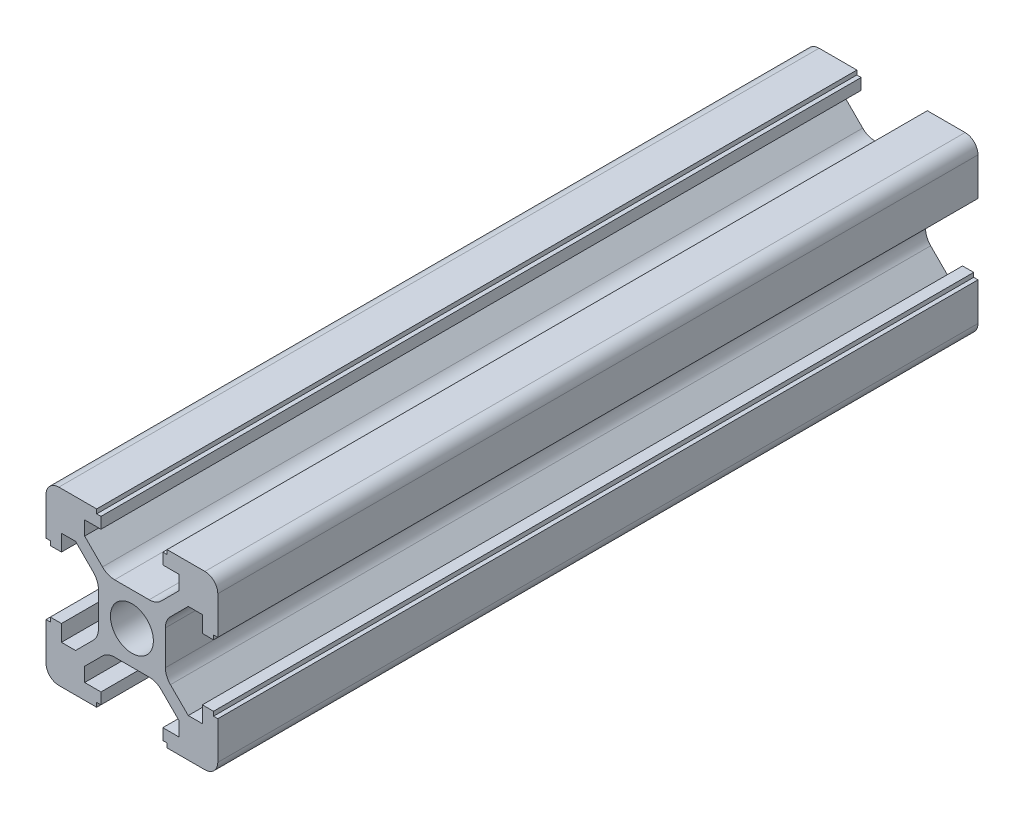
SolidWorks part; units mm, degrees
ref_plane "Front Plane" through (0, 0, 0) normal (0, 0, 1) x (1, 0, 0)
ref_plane "Top Plane" through (0, 0, 0) normal (0, 1, 0) x (1, 0, 0)
ref_plane "Right Plane" through (0, 0, 0) normal (1, 0, 0) x (0, 0, -1)
sketch "Sketch1" plane through (0, 0, 0) normal (0, 0, 1) x (1, 0, 0)
  line L0 (10, -4.1) -> (10, -8.5)
  line L1 (4.1, 10) -> (8.5, 10)
  line L2 (8.5, -10) -> (4.1, -10)
  line L3 (-8.5, -10) -> (-4.1, -10)
  line L4 (10, 8.5) -> (10, 4.1)
  line L7 (8.5, 10) -> (4.1, 10)
  line L8 (5.5, 6.5607) -> (3.4251, 4.4858)
  line L9 (8.5, 10) -> (4.1, 10)
  line L10 (3.9, 2.0109) -> (3.9, -2.0109)
  line L11 (2.0109, -3.9) -> (-2.0109, -3.9)
  line L12 (-3.9, -2.0109) -> (-3.9, 2.0109)
  line L13 (-2.0109, 3.9) -> (2.8393, 3.9)
  line L14 (2.5, 0) -> (22.2403, 0) construction
  line L15 (3.6, 9.5) -> (3.6, 8.2)
  line L16 (9.5, 3.6) -> (8.2, 3.6)
  line L17 (8.2, 3.6) -> (8.2, 5.5)
  line L18 (8.2, 5.5) -> (6.5607, 5.5)
  line L19 (10, -4.1) -> (10, -8.5)
  line L20 (4.1, 9.5) -> (3.6, 9.5)
  line L21 (4.1, 10) -> (4.1, 9.5)
  line L22 (8.5, 10) -> (4.1, 10)
  line L23 (10, 4.1) -> (9.5, 4.1)
  line L24 (9.5, 4.1) -> (9.5, 3.6)
  line L25 (5.5, 8.2) -> (5.5, 6.5607)
  line L26 (3.6, 8.2) -> (5.5, 8.2)
  line L27 (4.4858, 3.4251) -> (6.5607, 5.5)
  line L28 (10, -8.5) -> (10, -4.1)
  line L29 (6.5607, -5.5) -> (4.4858, -3.4251)
  line L30 (10, -8.5) -> (10, -4.1)
  line L31 (2.0109, -3.9) -> (-2.0109, -3.9)
  line L32 (3.9, 2.8393) -> (3.9, -2.0109)
  line L33 (9.5, -3.6) -> (8.2, -3.6)
  line L34 (3.6, -9.5) -> (3.6, -8.2)
  line L35 (3.6, -8.2) -> (5.5, -8.2)
  line L36 (5.5, -8.2) -> (5.5, -6.5607)
  line L37 (9.5, -4.1) -> (9.5, -3.6)
  line L38 (10, -4.1) -> (9.5, -4.1)
  line L39 (10, -8.5) -> (10, -4.1)
  line L40 (4.1, -10) -> (4.1, -9.5)
  line L41 (4.1, -9.5) -> (3.6, -9.5)
  line L42 (8.2, -5.5) -> (6.5607, -5.5)
  line L43 (8.2, -3.6) -> (8.2, -5.5)
  line L44 (3.4251, -4.4858) -> (5.5, -6.5607)
  line L45 (-4.1, -10) -> (-8.5, -10)
  line L46 (-10, -8.5) -> (-10, -4.1)
  line L47 (-8.5, -10) -> (-4.1, -10)
  line L48 (-5.5, -6.5607) -> (-3.4251, -4.4858)
  line L49 (-8.5, -10) -> (-4.1, -10)
  line L50 (-3.9, -2.0109) -> (-3.9, 2.0109)
  line L51 (2.0109, -3.9) -> (-2.0109, -3.9)
  line L52 (-3.6, -9.5) -> (-3.6, -8.2)
  line L53 (-9.5, -3.6) -> (-8.2, -3.6)
  line L54 (-8.2, -3.6) -> (-8.2, -5.5)
  line L55 (-8.2, -5.5) -> (-6.5607, -5.5)
  line L56 (-4.1, -9.5) -> (-3.6, -9.5)
  line L57 (-4.1, -10) -> (-4.1, -9.5)
  line L58 (-8.5, -10) -> (-4.1, -10)
  line L59 (-10, -4.1) -> (-9.5, -4.1)
  line L60 (-9.5, -4.1) -> (-9.5, -3.6)
  line L61 (-5.5, -8.2) -> (-5.5, -6.5607)
  line L62 (-3.6, -8.2) -> (-5.5, -8.2)
  line L63 (-4.4858, -3.4251) -> (-6.5607, -5.5)
  line L64 (-10, 4.1) -> (-10, 8.5)
  line L65 (-8.5, 10) -> (-4.1, 10)
  line L66 (-10, 8.5) -> (-10, 4.1)
  line L67 (-6.5607, 5.5) -> (-4.4858, 3.4251)
  line L68 (-10, 8.5) -> (-10, 4.1)
  line L69 (-2.0109, 3.9) -> (2.0109, 3.9)
  line L70 (-3.9, -2.0109) -> (-3.9, 2.0109)
  line L71 (-9.5, 3.6) -> (-8.2, 3.6)
  line L72 (-3.6, 9.5) -> (-3.6, 8.2)
  line L73 (-3.6, 8.2) -> (-5.5, 8.2)
  line L74 (-5.5, 8.2) -> (-5.5, 6.5607)
  line L75 (-9.5, 4.1) -> (-9.5, 3.6)
  line L76 (-10, 4.1) -> (-9.5, 4.1)
  line L77 (-10, 8.5) -> (-10, 4.1)
  line L78 (-4.1, 10) -> (-4.1, 9.5)
  line L79 (-4.1, 9.5) -> (-3.6, 9.5)
  line L80 (-8.2, 5.5) -> (-6.5607, 5.5)
  line L81 (-8.2, 3.6) -> (-8.2, 5.5)
  line L82 (-3.4251, 4.4858) -> (-5.5, 6.5607)
  line L83 (4.1, -10) -> (8.5, -10)
  arc A0 (2.0109, -3.9) -> (3.4251, -4.4858) centre (2.0109, -5.9) cw
  arc A1 (4.4858, -3.4251) -> (3.9, -2.0109) centre (5.9, -2.0109) cw
  arc A2 (3.9, 2.0109) -> (4.4858, 3.4251) centre (5.9, 2.0109) cw
  arc A3 (2.0109, 3.9) -> (3.4251, 4.4858) centre (2.0109, 5.9) ccw
  arc A4 (-2.0109, 3.9) -> (-3.4251, 4.4858) centre (-2.0109, 5.9) cw
  arc A5 (-4.4858, 3.4251) -> (-3.9, 2.0109) centre (-5.9, 2.0109) cw
  arc A6 (-3.4251, -4.4858) -> (-2.0109, -3.9) centre (-2.0109, -5.9) cw
  arc A7 (-3.9, -2.0109) -> (-4.4858, -3.4251) centre (-5.9, -2.0109) cw
  circle A8 centre (0, 0) radius 2.5
  arc A9 (-8.5, -10) -> (-10, -8.5) centre (-8.5, -8.5) cw
  arc A10 (-10, 8.5) -> (-8.5, 10) centre (-8.5, 8.5) cw
  arc A11 (8.5, 10) -> (10, 8.5) centre (8.5, 8.5) cw
  arc A12 (8.5, -10) -> (10, -8.5) centre (8.5, -8.5) ccw
  point P0 (0, 0)
  point P86 (0, 0)
  point P107 (10, -10)
  dimension "D3" = 2
  dimension "D5" = 5
  dimension "D2" = 1.5
  dimension "D8" = 1.5
  dimension "D4" = 6.1
  dimension "D6" = 4
  dimension "D11" = 0.5
  dimension "D12" = 0.5
extrude "Boss-Extrude2" add sketch "Sketch1" along normal blind 88.5
